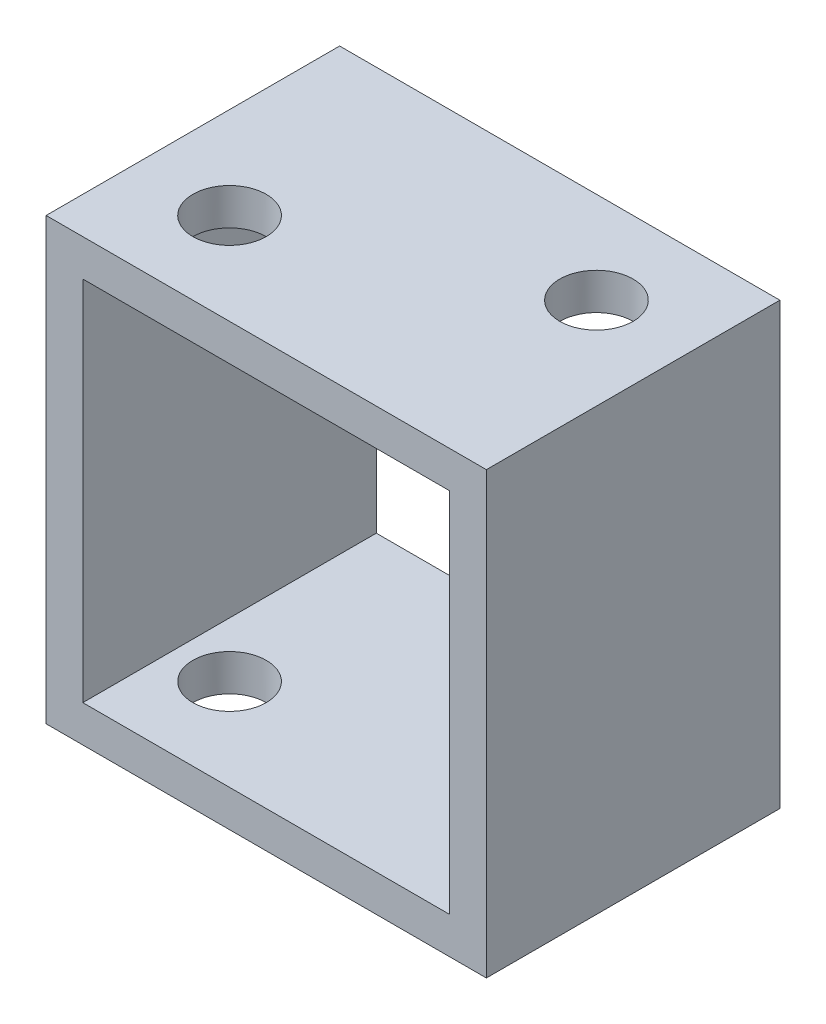
SolidWorks part; units mm, degrees
ref_plane "Front Plane" through (0, 0, 0) normal (0, 0, 1) x (1, 0, 0)
ref_plane "Top Plane" through (0, 0, 0) normal (0, 1, 0) x (1, 0, 0)
ref_plane "Right Plane" through (0, 0, 0) normal (1, 0, 0) x (0, 0, -1)
sketch "Sketch1" plane through (0, 0, 0) normal (0, 0, 1) x (1, 0, 0)
  line L0 (0, 0) -> (0, 38.1)
  line L1 (0, 38.1) -> (38.1, 38.1)
  line L2 (38.1, 38.1) -> (38.1, 0)
  line L3 (38.1, 0) -> (0, 0)
  line L4 (3.175, 34.925) -> (34.925, 34.925)
  line L5 (34.925, 34.925) -> (34.925, 3.175)
  line L6 (34.925, 3.175) -> (3.175, 3.175)
  line L7 (3.175, 3.175) -> (3.175, 34.925)
  dimension "D1" = 38.1
  dimension "D2" = 38.1
  dimension "D3" = 3.175
extrude "Boss-Extrude1" add sketch "Sketch1" along normal blind 25.4
sketch "Sketch2" plane through (0, 0, 0) normal (0, -1, 0) x (1, 0, 0)
  line L3 (38.1, 25.4) -> (38.1, 0) construction
  line L7 (0, 0) -> (38.1, 0) construction
  line L8 (0, 25.4) -> (38.1, 25.4) construction
  line L9 (0, 25.4) -> (0, 0) construction
  circle A0 centre (7.9375, 17.4625) radius 3.175
  circle A1 centre (30.1625, 7.9375) radius 3.175
  dimension "D1" = 6.35
  dimension "D2" = 7.9375
  dimension "D3" = 7.9375
  dimension "D4" = 7.9375
  dimension "D5" = 7.9375
extrude "Cut-Extrude1" cut sketch "Sketch2" against normal through all
equation "\"D2@Sketch2\"=(3/16)+(\"D1@Sketch2\"/2)"
equation "\"D3@Sketch2\"=\"D2@Sketch2\""
equation "\"D4@Sketch2\"=\"D2@Sketch2\""
